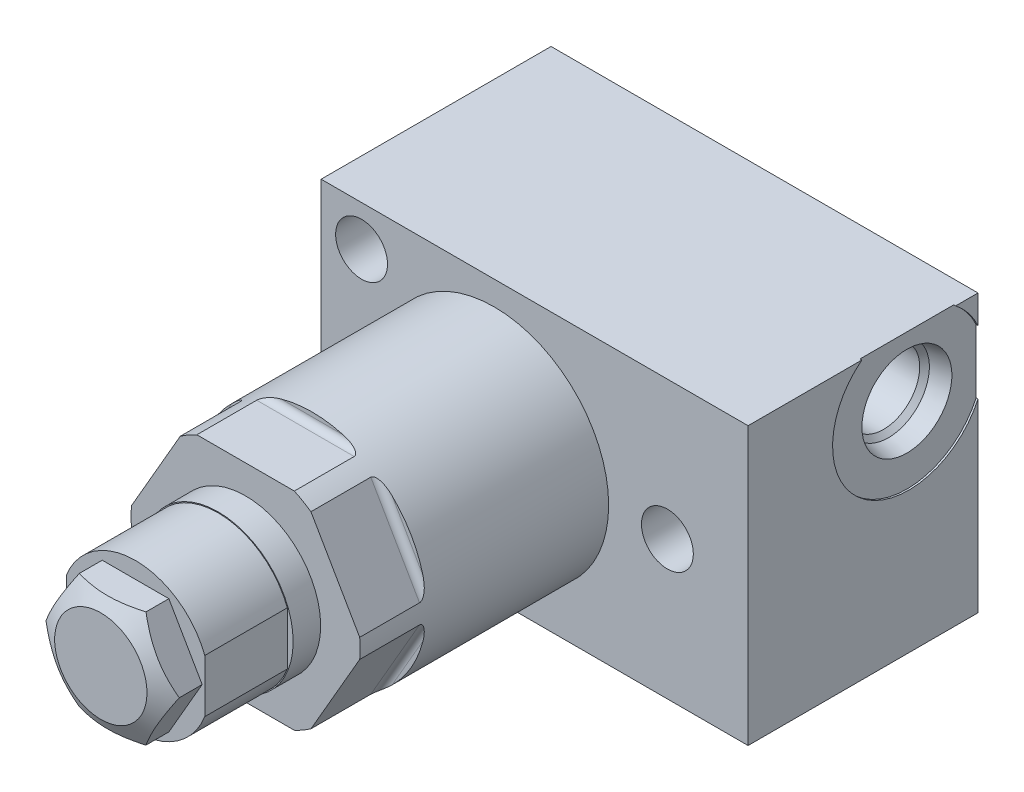
SolidWorks part; units mm, degrees
material "Alloy Steel"
ref_plane "Front" through (0, 0, 0) normal (0, 0, 1) x (1, 0, 0)
ref_plane "Top" through (0, 0, 0) normal (0, 1, 0) x (1, 0, 0)
ref_plane "Right" through (0, 0, 0) normal (1, 0, 0) x (0, 0, -1)
ref_plane "Plane1" through (0, 0, 0) normal (0, 0, 1) x (1, 0, 0)
ref_plane "Plane2" through (0, 0, 0) normal (0, 0, 1) x (1, 0, 0)
sketch "Sketch1" plane through (0, 0, 0) normal (0, 0, 1) x (1, 0, 0)
  circle A0 centre (0, 0) radius 15.748
  dimension "D1" = 31.496
extrude "Extrude1" add sketch "Sketch1" along normal blind 55.1434
ref_plane "Plane3" through (0, 0, 0) normal (1, 0, 0) x (0, 0, 1)
sketch "Sketch2" plane through (0, 0, 0) normal (1, 0, 0) x (0, 0, 1)
  line L0 (45.9994, 15.748) -> (45.9994, 15.1638)
  line L1 (46.9138, 14.2494) -> (55.1434, 14.2494)
  line L2 (45.6692, 0) -> (55.7276, 0) construction
  line L3 (55.1434, -15.748) -> (55.1434, 15.748) construction
  line L4 (45.9994, 15.748) -> (55.1434, 15.748)
  line L5 (55.1434, 15.748) -> (55.1434, 14.2494)
  arc A0 (45.9994, 15.1638) -> (46.9138, 14.2494) centre (46.9138, 15.1638) ccw
  dimension "D2" = 0.9144
  dimension "D1" = 28.4988
  dimension "D3" = 9.144
extrude "Cut-Extrude1" cut sketch "Sketch2" against normal mid plane 37.7952
ref_plane "Plane13" through (0, 0, 0) normal (1, 0, 0) x (0, 0, 1)
sketch "Sketch10" plane through (0, 0, 0) normal (1, 0, 0) x (0, 0, 1)
  line L0 (0, 14.8717) -> (7.7978, 14.8717)
  line L1 (7.7978, 14.8717) -> (8.6741, 15.748)
  line L2 (8.6741, 15.748) -> (0, 15.748)
  line L3 (0, 15.748) -> (0, 14.8717)
  line L4 (-0.4337, 0) -> (9.1078, 0) construction
  line L5 (45.9994, 15.748) -> (0, 15.748) construction
  line L6 (0, 15.748) -> (0, -15.748) construction
  dimension "D1" = 29.7434
  dimension "D2" = 45
  dimension "D3" = 7.7978
revolve "Cut-Revolve1" cut sketch "Sketch10" angle 360 about L4
ref_plane "Plane14" through (0, 0, 0) normal (1, 0, 0) x (0, 0, -1)
sketch "Sketch11" plane through (0, 0, 0) normal (1, 0, 0) x (0, 0, -1)
  line L0 (-55.1434, 0) -> (-70.2818, 0)
  line L1 (-70.2818, 0) -> (-70.2818, 10.3251)
  line L2 (-70.2818, 10.3251) -> (-55.1434, 10.3251)
  line L3 (-55.1434, 10.3251) -> (-55.1434, 0)
  line L4 (-71.1543, 0) -> (-36.7188, 0) construction
  line L5 (-55.1434, 15.748) -> (-55.1434, -14.2494) construction
  dimension "D1" = 20.6502
  dimension "D2" = 15.1384
revolve "Revolve1" add sketch "Sketch11" angle 360 about L4
ref_plane "Plane17" through (0, 0, 59.055) normal (0, 0, -1) x (0, 1, 0)
sketch "Sketch14" plane through (0, 0, 70.2818) normal (0, 0, -1) x (0, 1, 0)
  line L0 (-3.9852, 9.525) -> (3.9852, 9.525)
  line L1 (-3.9852, -9.525) -> (3.9852, -9.525)
  line L2 (-11.3576, 0) -> (11.3576, 0) construction
  arc A0 (3.9852, 9.525) -> (-3.9852, 9.525) centre (0, 0) ccw
  arc A1 (-3.9852, -9.525) -> (3.9852, -9.525) centre (0, 0) ccw
  dimension "D2" = 10.3251
  dimension "D1" = 19.05
extrude "Cut-Extrude10" cut sketch "Sketch14" along normal blind 11.3538
sketch "Sketch15" plane through (0, 0, 70.2818) normal (0, 0, 1) x (1, 0, 0)
  line L0 (-4.5827, 7.9375) -> (4.5827, 7.9375)
  line L1 (4.5827, 7.9375) -> (9.1654, 0)
  line L2 (9.1654, 0) -> (4.5827, -7.9375)
  line L3 (4.5827, -7.9375) -> (-4.5827, -7.9375)
  line L4 (-4.5827, -7.9375) -> (-9.1654, 0)
  line L5 (-9.1654, 0) -> (-4.5827, 7.9375)
  line L6 (-10.082, 0) -> (10.082, 0) construction
  dimension "D1" = 15.875
extrude "Extrude2" add sketch "Sketch15" along normal blind 4.7752
ref_plane "Plane18" through (0, 0, 0) normal (0, 1, 0) x (1, 0, 0)
sketch "Sketch16" plane through (0, 0, 0) normal (0, 1, 0) x (1, 0, 0)
  line L0 (6.35, -75.057) -> (9.1654, -73.4315)
  line L1 (0, -75.2653) -> (0, -73.4772) construction
  line L2 (9.1654, -73.4315) -> (9.1654, -75.057)
  line L3 (9.1654, -75.057) -> (6.35, -75.057)
  dimension "D1" = 30
  dimension "D2" = 12.7
revolve "Cut-Revolve3" cut sketch "Sketch16" angle 360 about L1
ref_plane "Plane19" through (0, 0, 0) normal (0, 1, 0) x (-1, 0, 0)
sketch "Sketch17" plane through (0, 0, 0) normal (0, 1, 0) x (-1, 0, 0)
  line L0 (-34.925, -10.668) -> (23.7998, -10.668)
  line L1 (23.7998, -10.668) -> (23.7998, 20.955)
  line L2 (23.7998, 20.955) -> (-34.925, 20.955)
  line L3 (-34.925, 20.955) -> (-34.925, -10.668)
  line L4 (-14.8717, 0) -> (14.8717, 0) construction
  dimension "D1" = 10.668
  dimension "D2" = 31.623
  dimension "D3" = 58.7248
  dimension "D4" = 23.7998
extrude "Extrude4" add sketch "Sketch17" along normal mid plane 38.1
ref_plane "Plane21" through (34.925, -19.05, 0) normal (1, 0, 0) x (0, 1, 0)
sketch "Sketch19" plane through (34.925, -19.05, 0) normal (1, 0, 0) x (0, 1, 0)
  line L0 (38.1, -10.668) -> (0, -10.668) construction
  circle A0 centre (29.845, -1.143) radius 10.4775
  dimension "D1" = 20.955
  dimension "D2" = 9.525
  dimension "D3" = 10.795
extrude "Cut-Extrude12" cut sketch "Sketch19" against normal blind 0.254
ref_plane "Plane22" through (34.671, 10.795, -1.143) normal (0, 0, 1) x (0, -1, 0)
sketch "S2D0001" plane through (34.671, 10.795, -1.143) normal (0, 0, 1) x (0, -1, 0)
  line L0 (0, 0) -> (6.1849, 0)
  line L1 (6.1849, 0) -> (5.6423, -2.5527)
  line L2 (5.6423, -2.5527) -> (4.9784, -3.2166)
  line L3 (4.9784, -3.2166) -> (4.9784, -17.272)
  line L4 (4.9784, -17.272) -> (0, -17.272)
  line L5 (0, -17.272) -> (0, 0)
  line L6 (0, -18.1356) -> (0, 0.8636) construction
  dimension "D1" = 17.272
revolve "Cut-Revolve4" cut sketch "S2D0001" angle 360 about L6
ref_plane "Plane23" through (0, 0, -9.3293) normal (0, 1, 0) x (-1, 0, 0)
sketch "Sketch21" plane through (0, 0, -9.3293) normal (0, 1, 0) x (-1, 0, 0)
  line L0 (0, -1.3387) -> (7.9375, -1.3387)
  line L1 (7.9375, -1.3387) -> (7.9375, 1.3283)
  line L2 (7.9375, 1.3283) -> (3.4544, 1.3283)
  line L3 (3.4544, 1.3283) -> (3.4544, 13.3933)
  line L4 (3.4544, 13.3933) -> (0, 15.4689)
  line L5 (0, 15.4689) -> (0, -1.3387)
  line L6 (0, -2.1791) -> (0, 16.3093) construction
revolve "Cut-Revolve5" cut sketch "Sketch21" angle 360 about L6
ref_plane "Plane24" through (0, 0, -9.3293) normal (0, 1, 0) x (-1, 0, 0)
sketch "Sketch22" plane through (0, 0, -9.3293) normal (0, 1, 0) x (-1, 0, 0)
  line L0 (0, -1.472) -> (0, 1.4617) construction
  circle A0 centre (-6.604, -0.0052) radius 1.3335
revolve "Revolve2" add sketch "Sketch22" angle 360 about L0
pattern_circular "CirPattern2" count 6 over 360 about axis through (0, 0, 0) along (0, 0, 1) of "Cut-Extrude1"
hole_wizard "Hole1" positions "Sketch24" profile "Sketch23" legacy end condition up to next
sketch "Sketch24" plane through (0, 0, 20.955) normal (0, 0, 1) x (1, 0, 0)
  line L0 (0, 0) -> (26.6789, 0) construction
  point P0 (-18.2626, -13.4874)
  point P6 (23.8252, 0)
  point P10 (-18.2372, 13.4874)
  dimension "D1" = 23.8252
  dimension "D2" = 13.4874
  dimension "D3" = 18.2626
  dimension "D4" = 18.2372
  dimension "D5" = 26.9748
sketch "Sketch23" plane through (-18.2626, -13.4874, 20.955) normal (1, 0, 0) x (0, -1, 0)
  line L0 (0, 0) -> (0, 31.623)
  line L1 (0, 31.623) -> (3.5687, 31.623)
  line L2 (3.5687, 31.623) -> (3.5687, 0)
  line L3 (3.5687, 0) -> (0, 0)
  line L4 (0, 110) -> (0, -10) construction
  dimension "Diameter" = 7.1374
  dimension "Depth" = 31.623
sketch "Sketch25" plane through (0, 0, 0) normal (1, 0, 0) x (0, 0, -1)
  line L0 (10.668, 0) -> (-75.057, 0) construction
  line L1 (50, 0) -> (-50, 0) construction
  line L2 (10.668, 6.4301) -> (10.668, -19.05) construction
  line L3 (-75.057, 6.35) -> (-75.057, -6.35) construction
  line L4 (-70.2818, 10.1981) -> (-58.928, 10.1981)
  line L5 (-70.2818, 10.3251) -> (-70.2818, 3.9852) construction
  line L6 (-58.928, 10.1981) -> (-58.928, 10.3251)
  line L7 (-55.1434, 10.3251) -> (-70.2818, 10.3251) construction
  line L8 (-58.928, 10.3251) -> (-70.2818, 10.3251)
  line L9 (-70.2818, 10.3251) -> (-70.2818, 10.1981)
  dimension "D1" = 11.3538
  dimension "D2" = 20.3962
revolve "Cut-Revolve6" cut sketch "Sketch25" angle 360 about L0
